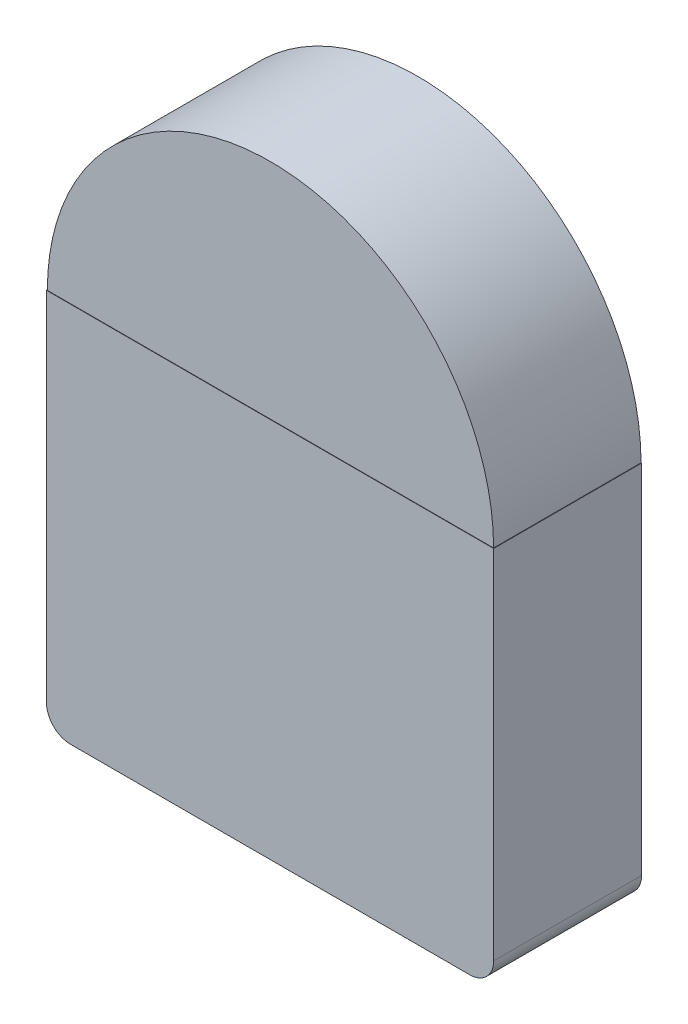
SolidWorks part; units mm, degrees
ref_plane "前视基准面" through (0, 0, 0) normal (0, 0, 1) x (1, 0, 0)
ref_plane "上视基准面" through (0, 0, 0) normal (0, 1, 0) x (1, 0, 0)
ref_plane "右视基准面" through (0, 0, 0) normal (1, 0, 0) x (0, 0, -1)
other "Configuration Table"
ref_plane "基准面1" through (0, 0, 0) normal (0, -1, 0) x (1, 0, 0)
sketch "草图1" plane through (0, 0, 0) normal (0, -1, 0) x (1, 0, 0)
  line L0 (-9.2913, 0) -> (-0.0013, 0)
  line L1 (-0.0013, 0) -> (-0.0013, 1.5)
  line L2 (-0.0013, 1.5) -> (-9.2913, 1.5)
  line L3 (-9.2913, 1.5) -> (-9.2913, 0)
  line L4 (-0.0013, 0) -> (-0.0013, 1.5025) construction
  dimension "D1" = 9.29
  dimension "D2" = 1.5
revolve "旋转1" add sketch "草图1" angle 180 about L4
sketch "草图2" plane through (0, 0, 1.5) normal (0, 0, 1) x (1, 0, 0)
  line L2 (-9.2913, 0) -> (9.2887, 0)
  line L3 (-9.2913, 0) -> (9.2887, 0)
  arc A1 (9.2887, 0) -> (-9.2913, 0) centre (-0.0013, 0) ccw
  arc A2 (9.2887, 0) -> (-9.2913, 0) centre (-0.0013, 0) ccw
  dimension "D1" = 0
extrude "凸台-拉伸1" add sketch "草图2" along normal blind 4.65
sketch "草图3" plane through (0, 0, 0) normal (0, -1, 0) x (1, 0, 0)
  line L0 (9.3087, 0) -> (-9.3113, 0)
  line L1 (-9.3113, 0) -> (-9.3113, 6.1567)
  line L2 (-9.3113, 6.1567) -> (9.3087, 6.1567)
  line L3 (9.3087, 6.1567) -> (9.3087, 0)
  line L4 (9.2887, 6.15) -> (9.2887, 0) construction
  line L5 (-9.2913, 6.15) -> (9.2913, 6.15) construction
  line L6 (-9.2913, 6.15) -> (-9.2913, 0) construction
  point P4 (9.4995, 6.1567)
  dimension "D1" = 0.02
  dimension "D2" = 6.15
  dimension "D3" = 0.02
extrude "凸台-拉伸2" add sketch "草图3" along normal blind 15.87
fillet "圆角1" radius 1 2 edges at (-9.3113, -15.87, 3.0783) (9.3087, -15.87, 3.0783)
sketch "草图4" plane through (0, 0, 6.15) normal (0, 0, 1) x (1, 0, 0)
  line L1 (-9.2913, 0) -> (9.2887, 0)
  line L2 (-9.2913, 0) -> (9.2887, 0)
  arc A5 (9.2887, 0) -> (-9.2913, 0) centre (-0.0013, 0) ccw
  arc A8 (9.2887, 0) -> (-9.2913, 0) centre (-0.0013, 0) ccw
  dimension "D1" = 0
extrude "切除-拉伸1" cut sketch "草图4" against normal blind 0.01
